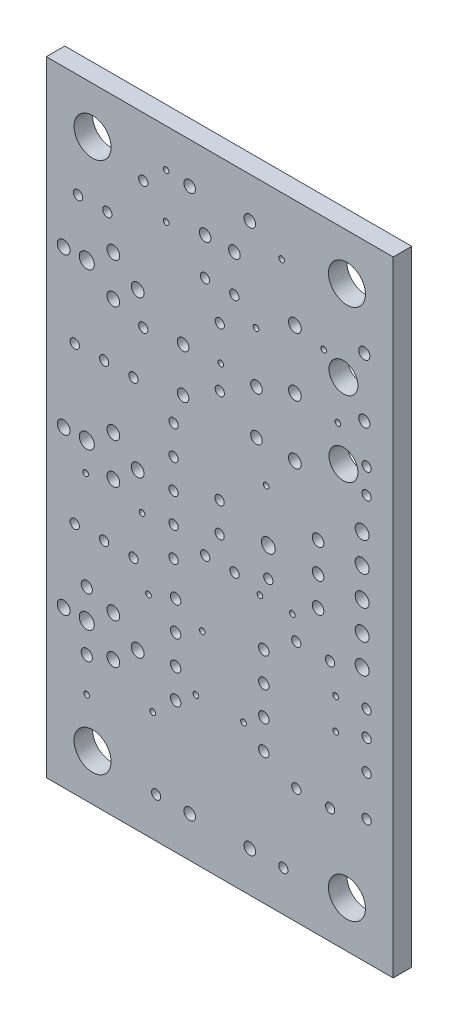
SolidWorks part; units mm, degrees
ref_plane "Plan de face" through (0, 0, 0) normal (0, 0, 1) x (1, 0, 0)
ref_plane "Plan de dessus" through (0, 0, 0) normal (0, 1, 0) x (1, 0, 0)
ref_plane "Plan de droite" through (0, 0, 0) normal (1, 0, 0) x (0, 0, -1)
sketch "Esquisse1" plane through (0, 0, 0) normal (0, 0, 1) x (1, 0, 0)
  line L0 (0, 0) -> (0, 54.0004)
  line L1 (0, 54.0004) -> (29.9999, 54.0004)
  line L2 (29.9999, 54.0004) -> (29.9999, 0)
  line L3 (29.9999, 0) -> (0, 0)
  circle A0 centre (18.1762, 38.3642) radius 0.5004
  circle A1 centre (18.1762, 34.5542) radius 0.5004
  circle A2 centre (11.8262, 34.5542) radius 0.5004
  circle A3 centre (11.8262, 38.3642) radius 0.5004
  circle A4 centre (17.5997, 3.5001) radius 0.5004
  circle A5 centre (12.4003, 3.5001) radius 0.5004
  circle A6 centre (12.4003, 50.5003) radius 0.5004
  circle A7 centre (17.5997, 50.5003) radius 0.5004
  circle A8 centre (3.5001, 10.9601) radius 0.4826
  circle A9 centre (3.5001, 16.0401) radius 0.4826
  circle A10 centre (27.5006, 40.4597) radius 0.4826
  circle A11 centre (27.5006, 45.5397) radius 0.4826
  circle A12 centre (16.2712, 47.5005) radius 0.5004
  circle A13 centre (13.7312, 47.5005) radius 0.5004
  circle A14 centre (27.7012, 14.2494) radius 0.3988
  circle A15 centre (27.7012, 10.7493) radius 0.3988
  circle A16 centre (1.4986, 13.5001) radius 0.5512
  circle A17 centre (7.8994, 13.5001) radius 0.5512
  circle A18 centre (5.7988, 11.75) radius 0.5512
  circle A19 centre (5.7988, 15.2502) radius 0.5512
  circle A20 centre (3.5001, 13.5001) radius 0.6502
  circle A21 centre (1.4986, 27.0002) radius 0.5512
  circle A22 centre (7.8994, 27.0002) radius 0.5512
  circle A23 centre (5.7988, 25.2501) radius 0.5512
  circle A24 centre (5.7988, 28.7503) radius 0.5512
  circle A25 centre (3.5001, 27.0002) radius 0.6502
  circle A26 centre (1.4986, 40.5003) radius 0.5512
  circle A27 centre (7.8994, 40.5003) radius 0.5512
  circle A28 centre (5.7988, 38.7502) radius 0.5512
  circle A29 centre (5.7988, 42.2504) radius 0.5512
  circle A30 centre (3.5001, 40.5003) radius 0.6502
  circle A31 centre (15.0012, 36.4592) radius 0.3988
  circle A32 centre (15.0012, 41.5392) radius 0.3988
  circle A33 centre (4.0005, 49.9999) radius 1.6002
  circle A34 centre (25.9994, 49.9999) radius 1.6002
  circle A35 centre (4.0005, 4.0005) radius 1.6002
  circle A36 centre (25.9994, 4.0005) radius 1.6002
  circle A37 centre (18.8062, 11.3843) radius 0.4496
  circle A38 centre (18.8062, 13.9243) radius 0.4496
  circle A39 centre (18.8062, 16.4643) radius 0.4496
  circle A40 centre (18.8062, 19.0043) radius 0.4496
  circle A41 centre (11.1862, 19.0043) radius 0.4496
  circle A42 centre (11.1862, 16.4643) radius 0.4496
  circle A43 centre (11.1862, 13.9243) radius 0.4496
  circle A44 centre (11.1862, 11.3843) radius 0.4496
  circle A45 centre (2.4613, 33.749) radius 0.3988
  circle A46 centre (5.0013, 33.749) radius 0.3988
  circle A47 centre (7.5413, 33.749) radius 0.3988
  circle A48 centre (2.4613, 20.2489) radius 0.3988
  circle A49 centre (5.0013, 20.2489) radius 0.3988
  circle A50 centre (7.5413, 20.2489) radius 0.3988
  circle A51 centre (5.2807, 45.0113) radius 0.3988
  circle A52 centre (2.7407, 45.0113) radius 0.3988
  circle A53 centre (14.9885, 28.2804) radius 0.3988
  circle A54 centre (14.9885, 25.7404) radius 0.3988
  circle A55 centre (16.2814, 23.5102) radius 0.3988
  circle A56 centre (13.7414, 23.5102) radius 0.3988
  circle A57 centre (13.7185, 44.2874) radius 0.3988
  circle A58 centre (16.2585, 44.2874) radius 0.3988
  circle A59 centre (21.4986, 44.6354) radius 0.5512
  circle A60 centre (21.4986, 39.5529) radius 0.5512
  circle A61 centre (21.4986, 34.4729) radius 0.5512
  circle A62 centre (25.6972, 42.8422) radius 1.2497
  circle A63 centre (25.6972, 36.3423) radius 1.2497
  circle A64 centre (23.5001, 29.5402) radius 0.5004
  circle A65 centre (23.5001, 27.0002) radius 0.5004
  circle A66 centre (23.5001, 24.4602) radius 0.5004
  circle A67 centre (20.5003, 3.5001) radius 0.3988
  circle A68 centre (9.4996, 3.5001) radius 0.3988
  circle A69 centre (8.3845, 48.9026) radius 0.3988
  circle A70 centre (8.3845, 37.9019) radius 0.3988
  circle A71 centre (21.6205, 10) radius 0.3988
  circle A72 centre (21.6205, 21.0007) radius 0.3988
  circle A73 centre (24.544, 10) radius 0.3988
  circle A74 centre (24.544, 21.0007) radius 0.3988
  circle A75 centre (27.7012, 16.8402) radius 0.3988
  circle A76 centre (27.7012, 37.1602) radius 0.3988
  circle A77 centre (27.7012, 18.9992) radius 0.3988
  circle A78 centre (27.7012, 35.0012) radius 0.3988
  circle A79 centre (27.3101, 27.0002) radius 0.5994
  circle A80 centre (27.3101, 29.5402) radius 0.5994
  circle A81 centre (27.3101, 32.0802) radius 0.5994
  circle A82 centre (27.3101, 24.4602) radius 0.5994
  circle A83 centre (27.3101, 21.9202) radius 0.5994
  circle A84 centre (19.1999, 27.0002) radius 0.5994
  circle A85 centre (19.1999, 24.5008) radius 0.3988
  circle A86 centre (11.0033, 32.07) radius 0.3988
  circle A87 centre (11.0033, 29.53) radius 0.3988
  circle A88 centre (11.0033, 26.99) radius 0.3988
  circle A89 centre (11.0033, 24.45) radius 0.3988
  circle A90 centre (11.0033, 21.91) radius 0.3988
  circle A91 centre (3.4036, 24.5161) radius 0.2438
  circle A92 centre (8.2804, 23.97) radius 0.2438
  circle A93 centre (8.8392, 18.1432) radius 0.2438
  circle A94 centre (13.4899, 17.719) radius 0.2438
  circle A95 centre (18.1331, 42.7558) radius 0.2438
  circle A96 centre (3.5001, 7.9731) radius 0.2438
  circle A97 centre (9.2075, 9.5275) radius 0.2438
  circle A98 centre (25.0266, 15.9766) radius 0.2438
  circle A99 centre (25.0266, 18.6233) radius 0.2438
  circle A100 centre (20.3556, 49.0068) radius 0.2438
  circle A101 centre (21.2801, 22.9133) radius 0.2438
  circle A102 centre (18.4734, 22.9133) radius 0.2438
  circle A103 centre (19.0094, 31.3817) radius 0.2438
  circle A104 centre (12.9311, 12.6721) radius 0.2438
  circle A105 centre (17.0561, 12.6721) radius 0.2438
  circle A106 centre (10.3607, 50.6933) radius 0.2438
  circle A107 centre (10.3607, 46.8147) radius 0.2438
  circle A108 centre (25.2146, 39.1897) radius 0.2438
  circle A109 centre (23.9903, 44.0563) radius 0.2438
  circle A110 centre (15.0901, 38.5724) radius 0.2438
extrude "Extrusion1" add sketch "Esquisse1" along normal blind 1.6
